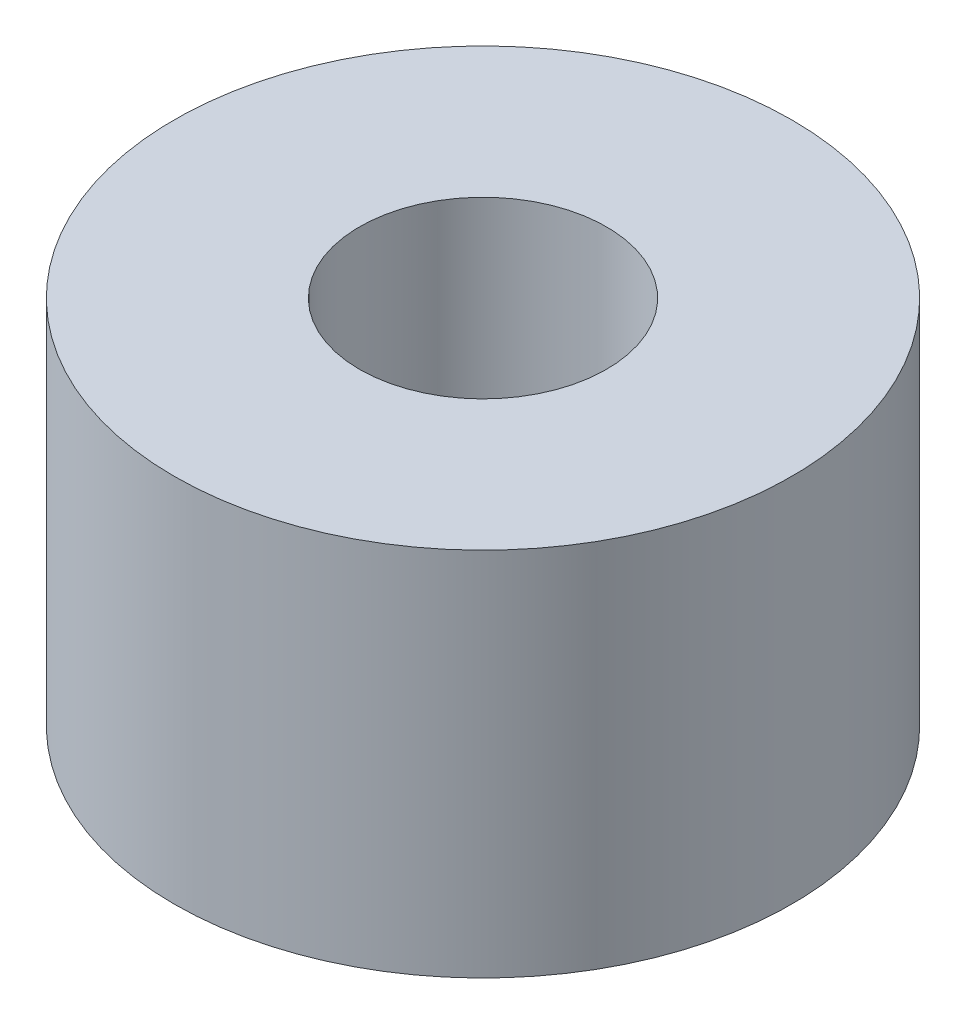
SolidWorks part; units mm, degrees
ref_plane "Front Plane" through (0, 0, 0) normal (0, 0, 1) x (1, 0, 0)
ref_plane "Top Plane" through (0, 0, 0) normal (0, 1, 0) x (1, 0, 0)
ref_plane "Right Plane" through (0, 0, 0) normal (1, 0, 0) x (0, 0, -1)
sketch "Sketch1" plane through (0, 0, 0) normal (0, 1, 0) x (1, 0, 0)
  circle A0 centre (0, 0) radius 4
  circle A1 centre (0, 0) radius 10
  dimension "D1" = 20
  dimension "D2" = 8
extrude "Boss-Extrude1" add sketch "Sketch1" against normal blind 12
